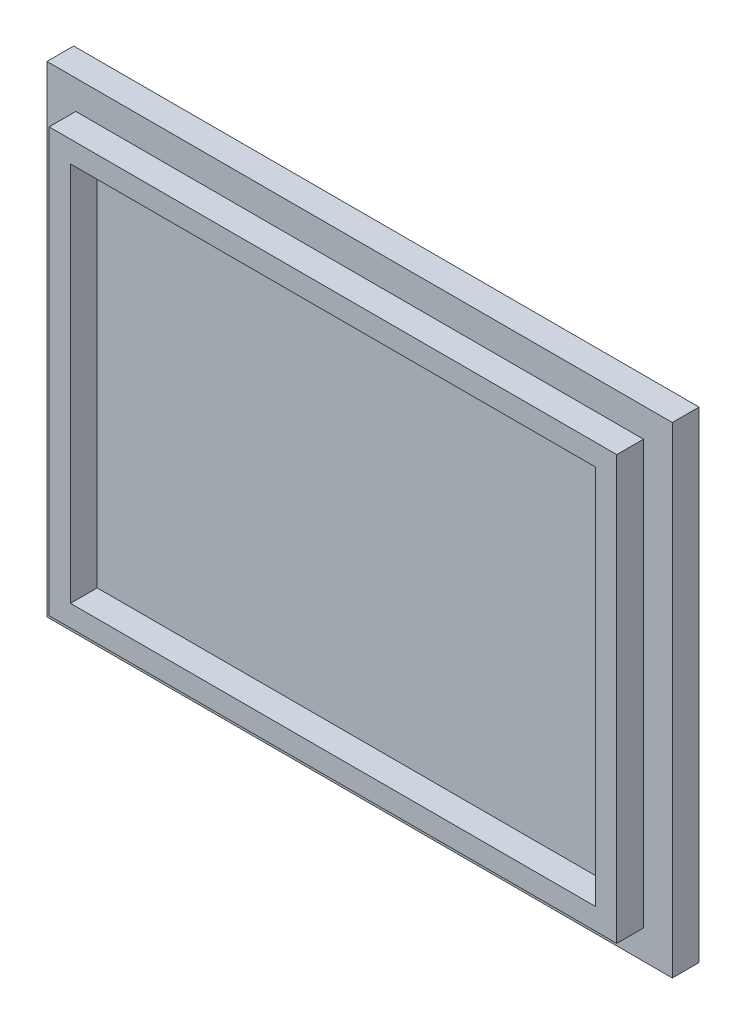
SolidWorks part; units mm, degrees
ref_plane "Front Plane" through (0, 0, 0) normal (0, 0, 1) x (1, 0, 0)
ref_plane "Top Plane" through (0, 0, 0) normal (0, 1, 0) x (1, 0, 0)
ref_plane "Right Plane" through (0, 0, 0) normal (1, 0, 0) x (0, 0, -1)
sketch "Sketch1" plane through (0, 0, 0) normal (0, 0, 1) x (1, 0, 0)
  line L1 (-74.295, -57.15) -> (74.295, -57.15)
  line L2 (-74.295, -57.15) -> (-74.295, 57.15)
  line L3 (-74.295, 57.15) -> (74.295, 57.15)
  line L4 (74.295, -57.15) -> (74.295, 57.15)
  line L5 (-74.295, -57.15) -> (74.295, 57.15) construction
  line L6 (-74.295, 57.15) -> (74.295, -57.15) construction
  point P0 (0, 0)
  dimension "D1" = 148.59
  dimension "D2" = 114.3
extrude "Boss-Extrude1" add sketch "Sketch1" along normal blind 6.35
sketch "Sketch2" plane through (0, 0, 6.35) normal (0, 0, 1) x (1, 0, 0)
  line L0 (74.295, -57.15) -> (74.295, 57.15) construction
  line L1 (-67.437, -50.292) -> (67.437, -50.292)
  line L2 (-67.437, -50.292) -> (-67.437, 50.292)
  line L3 (-67.437, 50.292) -> (67.437, 50.292)
  line L4 (67.437, -50.292) -> (67.437, 50.292)
  line L5 (-67.437, -50.292) -> (67.437, 50.292) construction
  line L6 (-67.437, 50.292) -> (67.437, -50.292) construction
  line L7 (-74.295, -57.15) -> (74.295, -57.15) construction
  line L8 (62.357, -45.212) -> (62.357, 45.212)
  line L9 (-62.357, 45.212) -> (62.357, 45.212)
  line L10 (-62.357, -45.212) -> (-62.357, 45.212)
  line L11 (-62.357, -45.212) -> (62.357, -45.212)
  point P0 (0, 0)
  dimension "D1" = 6.858
  dimension "D2" = 6.858
  dimension "D3" = 5.08
extrude "Boss-Extrude2" add sketch "Sketch2" along normal blind 6.35 contours L2 L1 L4 L3 | L8 L9 L10 L11
